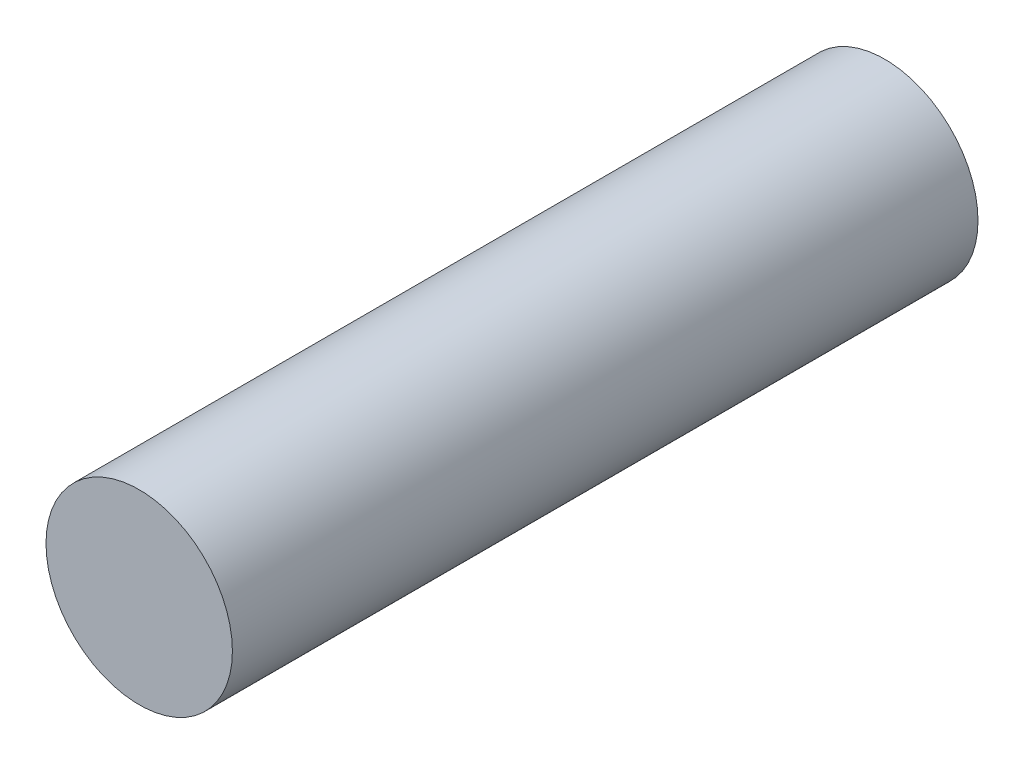
SolidWorks part; units mm, degrees
ref_plane "Alzado" through (0, 0, 0) normal (0, 0, 1) x (1, 0, 0)
ref_plane "Planta" through (0, 0, 0) normal (0, 1, 0) x (1, 0, 0)
ref_plane "Vista lateral" through (0, 0, 0) normal (1, 0, 0) x (0, 0, -1)
sketch "Croquis2" plane through (0, 0, 0) normal (0, 0, 1) x (1, 0, 0)
  circle A0 centre (0, 0) radius 10.5
  dimension "D1" = 21
extrude "Saliente-Extruir1" add sketch "Croquis2" along normal blind 84
